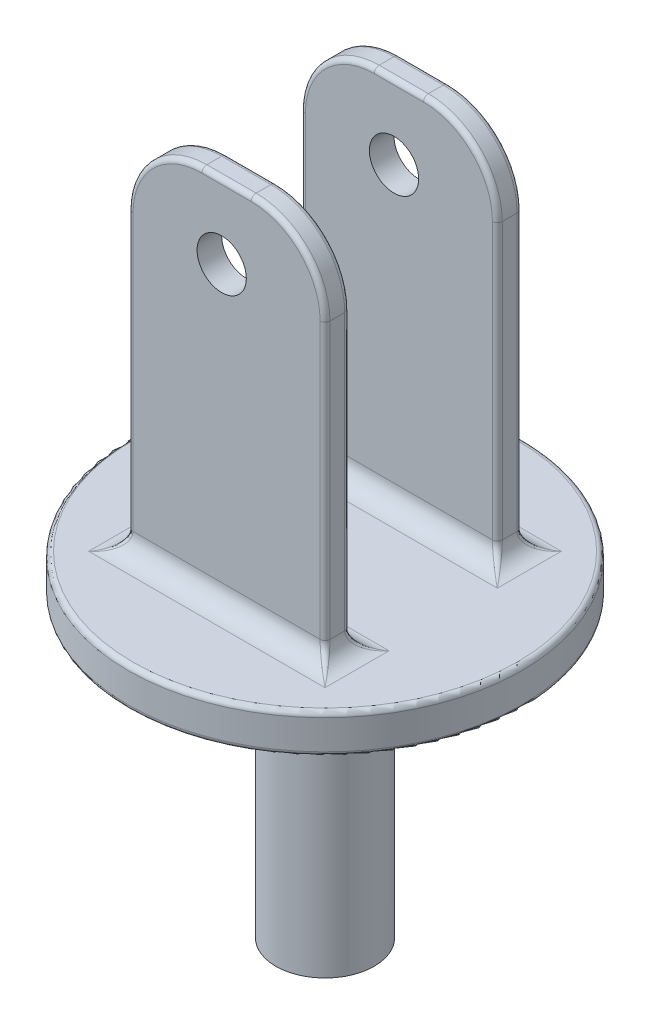
SolidWorks part; units mm, degrees
ref_plane "Front Plane" through (0, 0, 0) normal (0, 0, 1) x (1, 0, 0)
ref_plane "Top Plane" through (0, 0, 0) normal (0, 1, 0) x (1, 0, 0)
ref_plane "Right Plane" through (0, 0, 0) normal (1, 0, 0) x (0, 0, -1)
sketch "Sketch1" plane through (0, 0, 0) normal (0, 1, 0) x (1, 0, 0)
  circle A0 centre (0, 0) radius 40
  dimension "D1" = 80
extrude "Boss-Extrude1" add sketch "Sketch1" along normal blind 8 contours A0
sketch "Sketch2" plane through (0, 8, 0) normal (0, 1, 0) x (1, 0, 0)
  line L0 (0, 0) -> (0.1368, 39.9998) construction
  circle A0 centre (0, 0) radius 40 construction
sketch "Sketch4" plane through (0, 8, 0) normal (0, 1, 0) x (1, 0, 0)
  line L0 (20, 20) -> (-20, 20)
  line L5 (20, 20) -> (20, 15)
  line L6 (-20, 20) -> (-20, 15)
  line L7 (20, 15) -> (-20, 15)
  line L8 (20, 20) -> (-20, 15) construction
  line L9 (-20, 20) -> (20, 15) construction
  line L10 (0, 0) -> (0, 15) construction
  point P6 (0, 17.5)
  dimension "D1" = 15
  dimension "D3" = 40
  dimension "D4" = 5
extrude "Boss-Extrude5" add sketch "Sketch4" along normal blind 75
fillet "Fillet1" radius 15 2 edges at (20, 83, -17.5) (-20, 83, -17.5)
fillet "Fillet3" radius 4 4 edges at (-20, 8, -17.5) (0, 8, -15) (20, 8, -17.5) (0, 8, -20)
sketch "Sketch9" plane through (0, 0, -15) normal (0, 0, 1) x (1, 0, 0)
  line L1 (-5, 83) -> (5, 83) construction
  circle A0 centre (-0.9904, 68) radius 5
  dimension "D2" = 10
  dimension "D1" = 15
extrude "Cut-Extrude2" cut sketch "Sketch9" against normal blind 13
fillet "Fillet4" radius 1 14 edges at (21.1716, 9.1716, -21.1716) (-21.1716, 9.1716, -21.1716) (21.1716, 9.1716, -13.8284) (-21.1716, 9.1716, -13.8284) (-20, 40, -15) (20, 40, -15) (20, 40, -20) (15.6066, 78.6066, -20) (0, 83, -20) (-15.6066, 78.6066, -20) (-20, 40, -20) (15.6066, 78.6066, -15) (0, 83, -15) (-15.6066, 78.6066, -15)
mirror "Mirror2" about plane through (0, 0, 0) normal (0, 0, 1) of "Cut-Extrude2", "Fillet4", "Fillet1", "Boss-Extrude5", "Fillet3"
sketch "Sketch10" plane through (0, 0, 0) normal (0, -1, 0) x (1, 0, 0)
  circle A0 centre (0, 0) radius 7.5
  circle A1 centre (0, 0) radius 10
  dimension "D1" = 15
  dimension "D2" = 20
extrude "Boss-Extrude6" add sketch "Sketch10" along normal blind 60
fillet "Fillet5" radius 1 2 edges at (0, 0, 40) (0, 8, 40)
